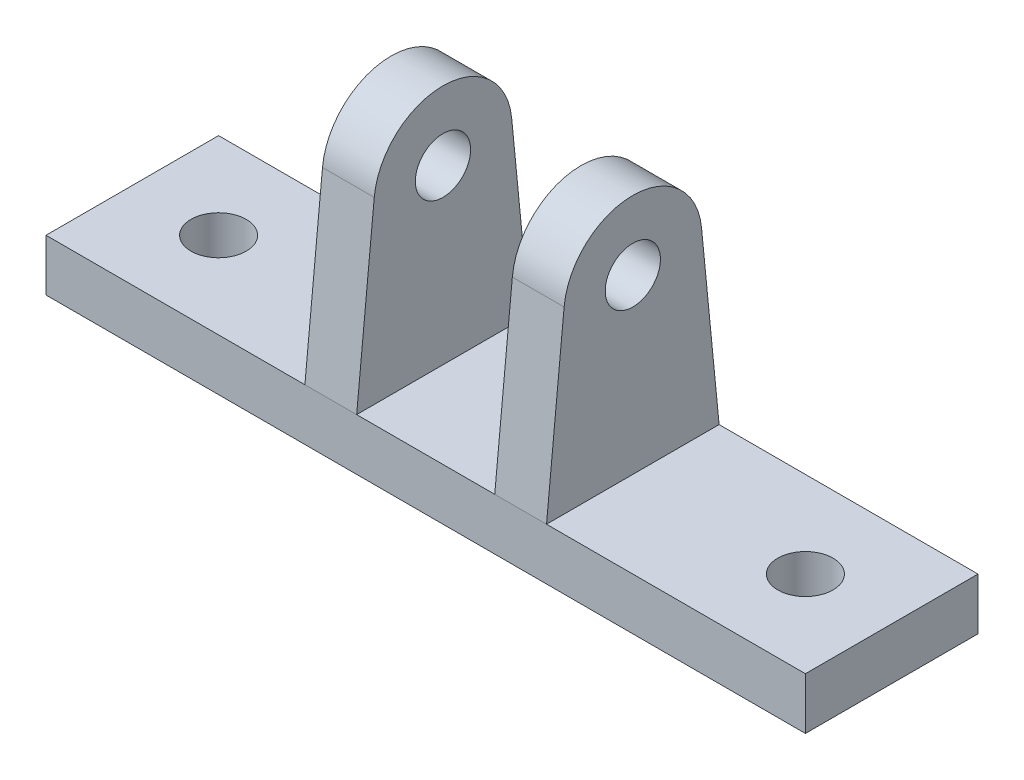
SolidWorks part; units mm, degrees
material "6061-T6 (SS)"
ref_plane "前视基准面" through (0, 0, 0) normal (0, 0, 1) x (1, 0, 0)
ref_plane "上视基准面" through (0, 0, 0) normal (0, 1, 0) x (1, 0, 0)
ref_plane "右视基准面" through (0, 0, 0) normal (1, 0, 0) x (0, 0, -1)
sketch "草图1" plane through (0, 0, 0) normal (0, 1, 0) x (1, 0, 0)
  line L0 (-17, 0) -> (17, 0)
  line L1 (-22, 5) -> (22, 5)
  line L2 (22, 5) -> (22, -5)
  line L3 (22, -5) -> (-22, -5)
  line L4 (-22, -5) -> (-22, 5)
  circle A0 centre (17, 0) radius 1.6
  circle A1 centre (-17, 0) radius 1.6
  point P4 (0, 0)
  point P10 (0, 5)
  point P13 (-22, 0)
  dimension "D2" = 3.2
  dimension "D1" = 34
  dimension "D3" = 44
  dimension "D4" = 10
extrude "凸台-拉伸1" add sketch "草图1" along normal blind 3
ref_plane "基准面1" through (4, 0, 0) normal (1, 0, 0) x (0, 0, -1)
sketch "草图2" plane through (4, 0, 0) normal (1, 0, 0) x (0, 0, -1)
  line L0 (5, 3) -> (-5, 3)
  line L1 (-5, 3) -> (-3.9809, 13.3904)
  line L2 (5, 3) -> (3.9809, 13.3904)
  circle A0 centre (0, 13) radius 1.6
  circle A1 centre (0, 13) radius 4
  dimension "D2" = 8
  dimension "D3" = 3.2
  dimension "D1" = 10
extrude "凸台-拉伸2" add sketch "草图2" along normal blind 3 contours A1 L1 L0 L2 | A1 A0
mirror "镜向1" about plane through (0, 0, 0) normal (1, 0, 0) of "凸台-拉伸2"
